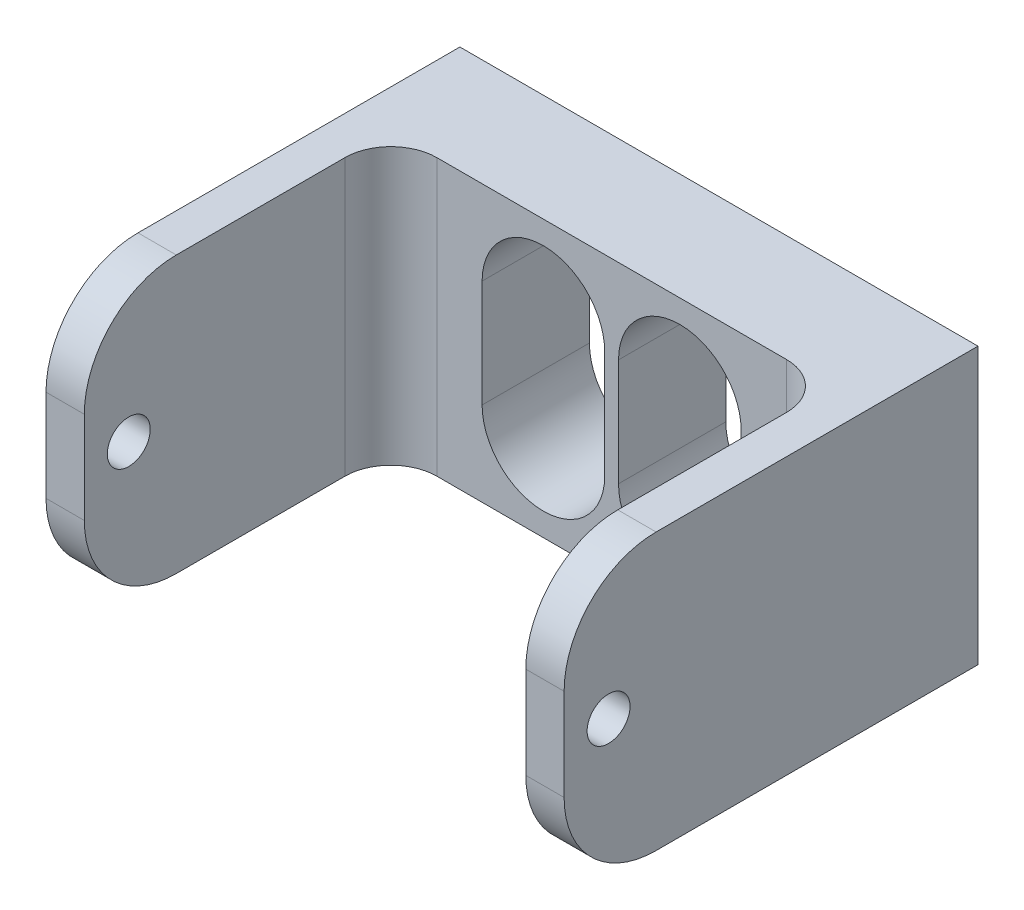
SolidWorks part; units mm, degrees
ref_plane "Front Plane" through (0, 0, 0) normal (0, 0, 1) x (1, 0, 0)
ref_plane "Top Plane" through (0, 0, 0) normal (0, 1, 0) x (1, 0, 0)
ref_plane "Right Plane" through (0, 0, 0) normal (1, 0, 0) x (0, 0, -1)
sketch "Sketch1" plane through (0, 0, 0) normal (0, 0, 1) x (1, 0, 0)
  line L0 (-4.45, 3.5) -> (-4.45, -3.5) construction
  line L1 (-16.9, -9) -> (16.9, -9)
  line L2 (-16.9, -9) -> (-16.9, 9)
  line L3 (-16.9, 9) -> (16.9, 9)
  line L4 (16.9, -9) -> (16.9, 9)
  line L5 (-16.9, -9) -> (16.9, 9) construction
  line L6 (-16.9, 9) -> (16.9, -9) construction
  line L7 (-0.45, 3.5) -> (-0.45, -3.5)
  line L8 (-8.45, 3.5) -> (-8.45, -3.5)
  line L9 (4.45, 3.5) -> (4.45, -3.5) construction
  line L10 (8.45, 3.5) -> (8.45, -3.5)
  line L11 (0.45, 3.5) -> (0.45, -3.5)
  arc A0 (-0.45, 3.5) -> (-8.45, 3.5) centre (-4.45, 3.5) ccw
  arc A1 (-8.45, -3.5) -> (-0.45, -3.5) centre (-4.45, -3.5) ccw
  arc A2 (8.45, 3.5) -> (0.45, 3.5) centre (4.45, 3.5) ccw
  arc A3 (0.45, -3.5) -> (8.45, -3.5) centre (4.45, -3.5) ccw
  point P0 (0, 0)
  point P8 (-4.45, 0)
  point P15 (4.45, 0)
  dimension "D1" = 33.8
  dimension "D2" = 18
  dimension "D3" = 8
  dimension "D4" = 7
  dimension "D5" = 8
  dimension "D6" = 7
  dimension "D7" = 16.9
  dimension "D8" = 4.45
extrude "Boss-Extrude1" add sketch "Sketch1" along normal blind 7
sketch "Sketch2" plane through (0, 0, 7) normal (0, 0, 1) x (1, 0, 0)
  line L0 (-16.9, -9) -> (16.9, -9) construction
  line L1 (-16.9, 9) -> (-14.4, 9)
  line L2 (-16.9, 9) -> (-16.9, -9)
  line L3 (-16.9, -9) -> (-14.4, -9)
  line L4 (-14.4, 9) -> (-14.4, -9)
  line L6 (16.9, 9) -> (14.4, 9)
  line L7 (16.9, 9) -> (16.9, -9)
  line L8 (16.9, -9) -> (14.4, -9)
  line L9 (14.4, 9) -> (14.4, -9)
  dimension "D1" = 2.5
  dimension "D2" = 2.5
extrude "Boss-Extrude2" add sketch "Sketch2" along normal blind 20
sketch "Sketch3" plane through (16.9, 0, 0) normal (1, 0, 0) x (0, 0, -1)
  line L0 (-27, -9) -> (-27, 9) construction
  circle A0 centre (-24.1, 0) radius 1.4
  point P2 (-27, 0)
  dimension "D1" = 2.8
  dimension "D2" = 2.9
extrude "Cut-Extrude1" cut sketch "Sketch3" against normal through all
fillet "Fillet1" radius 6 4 edges at (15.65, -9, 27) (-15.65, -9, 27) (-15.65, 9, 27) (15.65, 9, 27)
fillet "Fillet2" radius 3 2 edges at (14.4, 0, 7)
